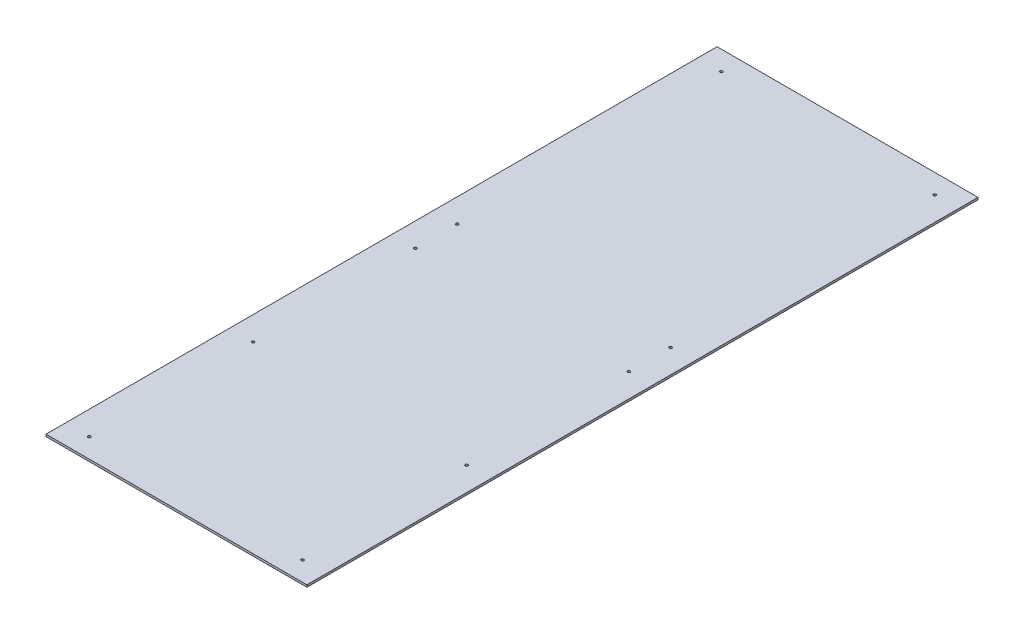
SolidWorks part; units mm, degrees
material "PC High Viscosity"
ref_plane "Front Plane" through (0, 0, 0) normal (0, 0, 1) x (1, 0, 0)
ref_plane "Top Plane" through (0, 0, 0) normal (0, 1, 0) x (1, 0, 0)
ref_plane "Right Plane" through (0, 0, 0) normal (1, 0, 0) x (0, 0, -1)
sketch "Sketch1" plane through (0, 0, 0) normal (0, 1, 0) x (1, 0, 0)
  line L1 (383.921, -987.425) -> (-383.921, -987.425)
  line L2 (383.921, -987.425) -> (383.921, 987.425)
  line L3 (383.921, 987.425) -> (-383.921, 987.425)
  line L4 (-383.921, -987.425) -> (-383.921, 987.425)
  line L5 (383.921, -987.425) -> (-383.921, 987.425) construction
  line L6 (383.921, 987.425) -> (-383.921, -987.425) construction
  point P0 (0, 0)
  dimension "D1" = 767.842
  dimension "D2" = 1974.85
extrude "Boss-Extrude1" add sketch "Sketch1" along normal blind 6.35
hole_wizard "J (0.277) Diameter Hole1" positions "Sketch4" profile "Sketch5" hole size "O" standard "ANSI Inch" end condition through all
sketch "Sketch4" plane through (0, 0, 0) normal (0, -1, 0) x (-1, 0, 0)
  line L0 (-383.921, 987.425) -> (383.921, 987.425) construction
  line L1 (-383.921, -987.425) -> (-383.921, 987.425) construction
  line L3 (383.921, -987.425) -> (-383.921, -987.425) construction
  line L4 (383.921, 987.425) -> (383.921, -987.425) construction
  point P0 (-314.071, -930.275)
  point P6 (313.944, -930.275)
  point P9 (-314.071, 29.6337)
  point P12 (314.071, 29.6337)
  point P15 (313.944, 930.275)
  point P18 (-314.071, 930.275)
  point P34 (-314.071, 152.7694)
  point P36 (314.071, 152.7694)
  point P40 (-314.071, -447.6112)
  point P42 (314.071, -447.6112)
  dimension "D2" = 477.2449
  dimension "D3" = 628.015
  dimension "D4" = 69.85
  dimension "D5" = 57.15
  dimension "D6" = 69.85
  dimension "D7" = 628.015
  dimension "D8" = 69.85
  dimension "D9" = 69.85
  dimension "D10" = 777.5056
  dimension "D11" = 123.1357
  dimension "D14" = 57.15
sketch "Sketch5" plane through (314.071, 0, 930.275) normal (1, 0, 0) x (0, 0, -1)
  line L0 (0, 0) -> (0, 6.35)
  line L1 (0, 6.35) -> (4.0132, 6.35)
  line L2 (4.0132, 6.35) -> (4.0132, 0)
  line L5 (4.0132, 0) -> (0, 0)
  line L11 (0, -6.35) -> (0, 107.95) construction
  dimension "Thru Hole Dia." = 8.0264
  dimension "Thru Hole Depth" = 6.35
